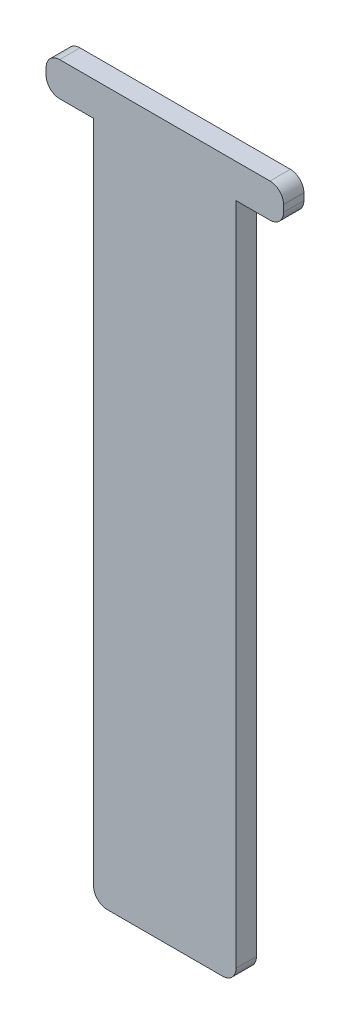
SolidWorks part; units mm, degrees
ref_plane "Front Plane" through (0, 0, 0) normal (0, 0, 1) x (1, 0, 0)
ref_plane "Top Plane" through (0, 0, 0) normal (0, 1, 0) x (1, 0, 0)
ref_plane "Right Plane" through (0, 0, 0) normal (1, 0, 0) x (0, 0, -1)
sketch "Sketch1" plane through (0, 0, 0) normal (0, 0, 1) x (1, 0, 0)
  line L0 (-16.761, 91.0574) -> (14.239, 91.0574)
  line L1 (16.239, 89.0574) -> (16.239, 88.0574)
  line L2 (14.239, 86.0574) -> (9.239, 86.0574)
  line L3 (9.239, 86.0574) -> (9.239, -11.9426)
  line L4 (7.239, -13.9426) -> (-9.761, -13.9426)
  line L5 (-11.761, -11.9426) -> (-11.761, 86.0574)
  line L6 (-11.761, 86.0574) -> (-16.761, 86.0574)
  line L7 (-18.761, 88.0574) -> (-18.761, 89.0574)
  arc A0 (-9.761, -13.9426) -> (-11.761, -11.9426) centre (-9.761, -11.9426) cw
  arc A1 (7.239, -13.9426) -> (9.239, -11.9426) centre (7.239, -11.9426) ccw
  arc A2 (-16.761, 86.0574) -> (-18.761, 88.0574) centre (-16.761, 88.0574) cw
  arc A3 (-16.761, 91.0574) -> (-18.761, 89.0574) centre (-16.761, 89.0574) ccw
  arc A4 (16.239, 89.0574) -> (14.239, 91.0574) centre (14.239, 89.0574) ccw
  arc A5 (14.239, 86.0574) -> (16.239, 88.0574) centre (14.239, 88.0574) ccw
  point P10 (-11.761, -13.9426)
  point P13 (9.239, -13.9426)
  point P16 (-18.761, 86.0574)
  point P19 (-18.761, 91.0574)
  point P22 (16.239, 91.0574)
  dimension "D5" = 2
  dimension "D1" = 21
  dimension "D2" = 35
  dimension "D3" = 5
  dimension "D4" = 100
extrude "Boss-Extrude1" add sketch "Sketch1" along normal blind 3
